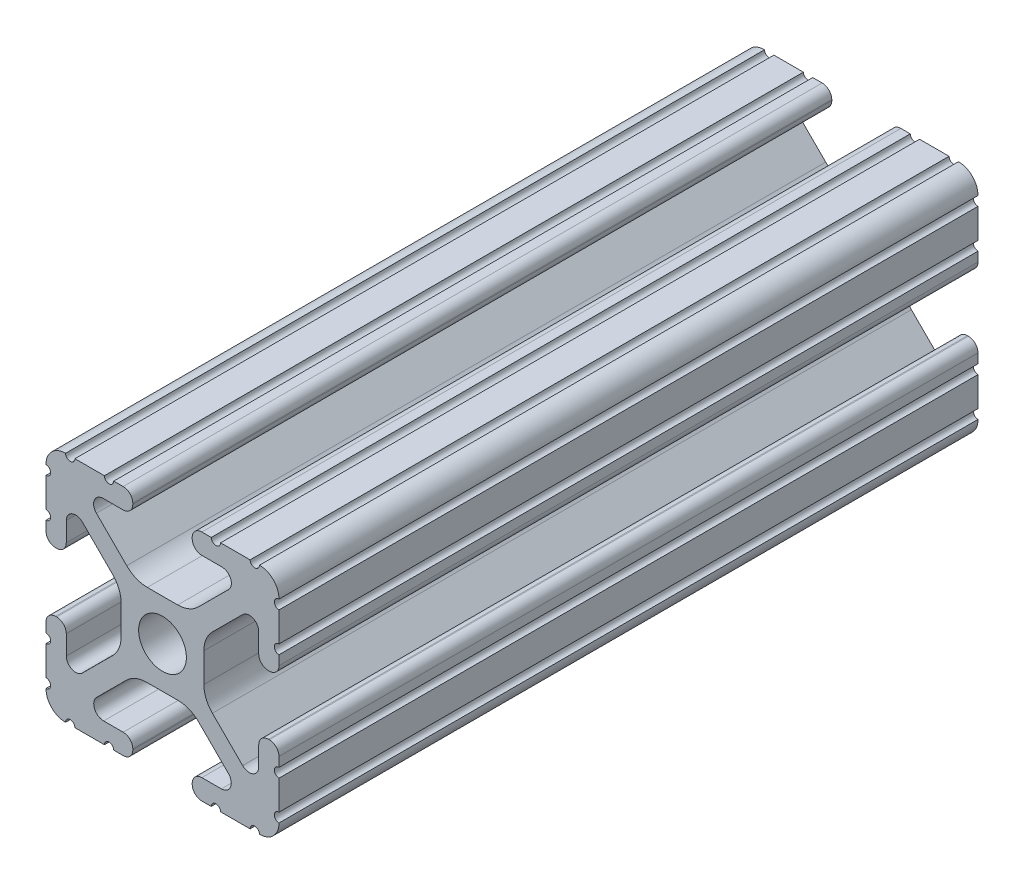
SolidWorks part; units mm, degrees
material "6061 Alloy"
ref_plane "Front Plane" through (0, 0, 0) normal (0, 0, 1) x (1, 0, 0)
ref_plane "Top Plane" through (0, 0, 0) normal (0, 1, 0) x (1, 0, 0)
ref_plane "Right Plane" through (0, 0, 0) normal (1, 0, 0) x (0, 0, -1)
sketch "Sketch1" plane through (0, 0, 0) normal (0, 0, 1) x (1, 0, 0)
  line L0 (-7.2072, 8.7245) -> (-3.9003, 5.4237)
  line L1 (-4.2875, 10.4902) -> (-6.4768, 10.4902)
  line L2 (-3.2384, 11.651) -> (-3.2384, 11.5392)
  line L3 (-5.3171, 12.7) -> (-4.2875, 12.7)
  line L4 (0, 13.4005) -> (0, -14.8534) construction
  line L5 (12.7, 0) -> (-13.9989, 0) construction
  line L6 (-9.5504, 12.7) -> (-6.3331, 12.7)
  line L7 (-12.7, 6.3331) -> (-12.7, 9.5504)
  line L8 (-12.7, 4.2875) -> (-12.7, 5.3171)
  line L9 (-11.5392, 3.2385) -> (-11.651, 3.2385)
  line L10 (-10.4902, 6.4021) -> (-10.4902, 4.2875)
  line L11 (-5.4405, 3.8388) -> (-8.737, 7.1292)
  line L12 (-4.5085, -1.5917) -> (-4.5085, 1.5917)
  line L13 (-1.7093, -4.4958) -> (1.7093, -4.4958)
  line L14 (3.9523, -5.4237) -> (7.1797, -8.6452)
  line L15 (6.4164, -10.4902) -> (4.2875, -10.4902)
  line L16 (3.2385, -11.5392) -> (3.2385, -11.651)
  line L17 (4.2875, -12.7) -> (5.3171, -12.7)
  line L18 (6.3331, -12.7) -> (9.5504, -12.7)
  line L19 (12.7, -9.5504) -> (12.7, -6.3331)
  line L20 (12.7, -5.3171) -> (12.7, -4.2875)
  line L21 (11.651, -3.2385) -> (11.5392, -3.2385)
  line L22 (10.4902, -4.2875) -> (10.4902, -6.4021)
  line L23 (8.737, -7.1292) -> (5.4405, -3.8388)
  line L24 (4.5085, -1.5917) -> (4.5085, 1.5917)
  line L25 (5.4405, 3.8388) -> (8.737, 7.1292)
  line L26 (10.4902, 6.4021) -> (10.4902, 4.2875)
  line L27 (11.5392, 3.2385) -> (11.651, 3.2385)
  line L28 (12.7, 4.2875) -> (12.7, 5.3171)
  line L29 (12.7, 6.3331) -> (12.7, 9.5504)
  line L30 (9.5504, 12.7) -> (6.3331, 12.7)
  line L31 (5.3171, 12.7) -> (4.2875, 12.7)
  line L32 (3.2384, 11.651) -> (3.2384, 11.5392)
  line L33 (4.2875, 10.4902) -> (6.4768, 10.4902)
  line L34 (7.2072, 8.7245) -> (3.9003, 5.4237)
  line L35 (1.6573, 4.4958) -> (-1.6573, 4.4958)
  line L36 (-8.737, -7.1292) -> (-5.4405, -3.8388)
  line L37 (-10.4902, -4.2875) -> (-10.4902, -6.4021)
  line L38 (-11.651, -3.2385) -> (-11.5392, -3.2385)
  line L39 (-12.7, -5.3171) -> (-12.7, -4.2875)
  line L40 (-12.7, -9.5504) -> (-12.7, -6.3331)
  line L41 (-6.3331, -12.7) -> (-9.5504, -12.7)
  line L42 (-4.2875, -12.7) -> (-5.3171, -12.7)
  line L43 (-3.2385, -11.5392) -> (-3.2385, -11.651)
  line L44 (-6.4164, -10.4902) -> (-4.2875, -10.4902)
  line L45 (-3.9523, -5.4237) -> (-7.1797, -8.6452)
  arc A0 (-7.2072, 8.7245) -> (-6.4768, 10.4902) centre (-6.4768, 9.4563) cw
  arc A1 (-3.2384, 11.5392) -> (-4.2875, 10.4902) centre (-4.2875, 11.5392) cw
  arc A2 (-4.2875, 12.7) -> (-3.2384, 11.651) centre (-4.2875, 11.651) cw
  arc A3 (-5.3171, 12.7) -> (-6.3331, 12.7) centre (-5.8251, 12.7) cw
  arc A4 (-9.5504, 12.7) -> (-10.5664, 12.6998) centre (-10.0584, 12.7) cw
  arc A5 (-12.6998, 10.5664) -> (-10.5664, 12.6998) centre (-10.5918, 10.5918) cw
  arc A6 (-12.6998, 10.5664) -> (-12.7, 9.5504) centre (-12.7, 10.0584) cw
  arc A7 (-12.7, 6.3331) -> (-12.7, 5.3171) centre (-12.7, 5.8251) cw
  arc A8 (-11.651, 3.2385) -> (-12.7, 4.2875) centre (-11.651, 4.2875) cw
  arc A9 (-10.4902, 4.2875) -> (-11.5392, 3.2385) centre (-11.5392, 4.2875) cw
  circle A10 centre (0, 0) radius 2.6035
  arc A11 (-10.4902, 6.4021) -> (-8.737, 7.1292) centre (-9.4628, 6.4021) cw
  arc A12 (-5.4405, 3.8388) -> (-4.5085, 1.5917) centre (-7.6835, 1.5917) cw
  arc A13 (-4.5085, -1.5917) -> (-5.4405, -3.8388) centre (-7.6835, -1.5917) cw
  arc A14 (-8.737, -7.1292) -> (-10.4902, -6.4021) centre (-9.4628, -6.4021) cw
  arc A15 (-1.7093, -4.4958) -> (-3.9523, -5.4237) centre (-1.7093, -7.6708) ccw
  arc A16 (3.9523, -5.4237) -> (1.7093, -4.4958) centre (1.7093, -7.6708) ccw
  arc A17 (6.4164, -10.4902) -> (7.1797, -8.6452) centre (6.4164, -9.4098) ccw
  arc A18 (4.2875, -10.4902) -> (3.2385, -11.5392) centre (4.2875, -11.5392) ccw
  arc A19 (3.2385, -11.651) -> (4.2875, -12.7) centre (4.2875, -11.651) ccw
  arc A20 (6.3331, -12.7) -> (5.3171, -12.7) centre (5.8251, -12.7) ccw
  arc A21 (10.5664, -12.6998) -> (9.5504, -12.7) centre (10.0584, -12.7) ccw
  arc A22 (10.5664, -12.6998) -> (12.6998, -10.5664) centre (10.5918, -10.5918) ccw
  arc A23 (12.7, -9.5504) -> (12.6998, -10.5664) centre (12.7, -10.0584) ccw
  arc A24 (12.7, -5.3171) -> (12.7, -6.3331) centre (12.7, -5.8251) ccw
  arc A25 (12.7, -4.2875) -> (11.651, -3.2385) centre (11.651, -4.2875) ccw
  arc A26 (11.5392, -3.2385) -> (10.4902, -4.2875) centre (11.5392, -4.2875) ccw
  arc A27 (8.737, -7.1292) -> (10.4902, -6.4021) centre (9.4628, -6.4021) ccw
  arc A28 (4.5085, -1.5917) -> (5.4405, -3.8388) centre (7.6835, -1.5917) ccw
  arc A29 (5.4405, 3.8388) -> (4.5085, 1.5917) centre (7.6835, 1.5917) ccw
  arc A30 (10.4902, 6.4021) -> (8.737, 7.1292) centre (9.4628, 6.4021) ccw
  arc A31 (10.4902, 4.2875) -> (11.5392, 3.2385) centre (11.5392, 4.2875) ccw
  arc A32 (11.651, 3.2385) -> (12.7, 4.2875) centre (11.651, 4.2875) ccw
  arc A33 (12.7, 6.3331) -> (12.7, 5.3171) centre (12.7, 5.8251) ccw
  arc A34 (12.6998, 10.5664) -> (12.7, 9.5504) centre (12.7, 10.0584) ccw
  arc A35 (12.6998, 10.5664) -> (10.5664, 12.6998) centre (10.5918, 10.5918) ccw
  arc A36 (9.5504, 12.7) -> (10.5664, 12.6998) centre (10.0584, 12.7) ccw
  arc A37 (5.3171, 12.7) -> (6.3331, 12.7) centre (5.8251, 12.7) ccw
  arc A38 (4.2875, 12.7) -> (3.2384, 11.651) centre (4.2875, 11.651) ccw
  arc A39 (3.2384, 11.5392) -> (4.2875, 10.4902) centre (4.2875, 11.5392) ccw
  arc A40 (7.2072, 8.7245) -> (6.4768, 10.4902) centre (6.4768, 9.4563) ccw
  arc A41 (1.6573, 4.4958) -> (3.9003, 5.4237) centre (1.6573, 7.6708) ccw
  arc A42 (-1.6573, 4.4958) -> (-3.9003, 5.4237) centre (-1.6573, 7.6708) cw
  arc A43 (-11.5392, -3.2385) -> (-10.4902, -4.2875) centre (-11.5392, -4.2875) cw
  arc A44 (-12.7, -4.2875) -> (-11.651, -3.2385) centre (-11.651, -4.2875) cw
  arc A45 (-12.7, -5.3171) -> (-12.7, -6.3331) centre (-12.7, -5.8251) cw
  arc A46 (-12.7, -9.5504) -> (-12.6998, -10.5664) centre (-12.7, -10.0584) cw
  arc A47 (-10.5664, -12.6998) -> (-12.6998, -10.5664) centre (-10.5918, -10.5918) cw
  arc A48 (-10.5664, -12.6998) -> (-9.5504, -12.7) centre (-10.0584, -12.7) cw
  arc A49 (-6.3331, -12.7) -> (-5.3171, -12.7) centre (-5.8251, -12.7) cw
  arc A50 (-3.2385, -11.651) -> (-4.2875, -12.7) centre (-4.2875, -11.651) cw
  arc A51 (-4.2875, -10.4902) -> (-3.2385, -11.5392) centre (-4.2875, -11.5392) cw
  arc A52 (-6.4164, -10.4902) -> (-7.1797, -8.6452) centre (-6.4164, -9.4098) cw
  dimension "D1" = 5.207
  dimension "D9" = 14.859
  dimension "D2" = 25.4
  dimension "D3" = 12.7
  dimension "D4" = 6.477
  dimension "D5" = 8.2042
  dimension "D6" = 9.017
  dimension "D8" = 2.2098
  dimension "D10" = 2.2098
extrude "Extrude1" add sketch "Sketch1" against normal blind 76.2
